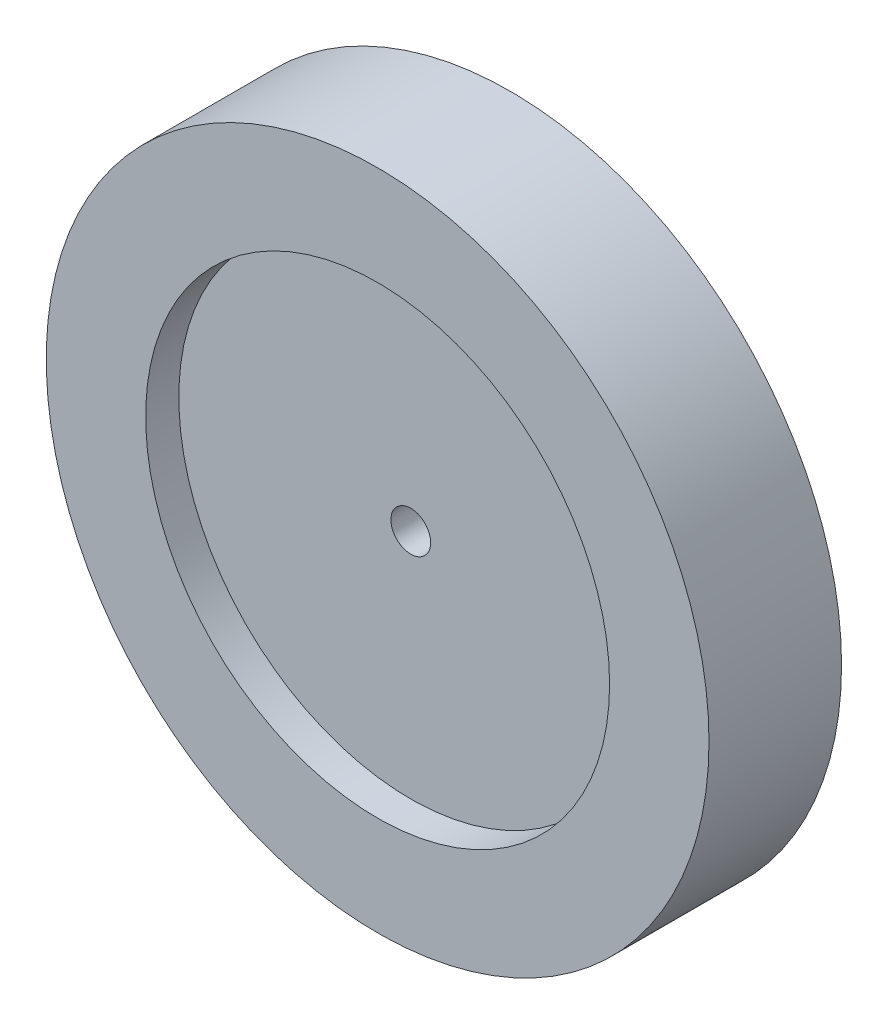
SolidWorks part; units mm, degrees
ref_plane "Front Plane" through (0, 0, 0) normal (0, 0, 1) x (1, 0, 0)
ref_plane "Top Plane" through (0, 0, 0) normal (0, 1, 0) x (1, 0, 0)
ref_plane "Right Plane" through (0, 0, 0) normal (1, 0, 0) x (0, 0, -1)
sketch "Sketch1" plane through (0, 0, 0) normal (0, 0, 1) x (1, 0, 0)
  circle A0 centre (0, 0) radius 50
  dimension "D1" = 100
extrude "Boss-Extrude1" add sketch "Sketch1" along normal mid plane 20
sketch "Sketch2" plane through (0, 0, 10) normal (0, 0, 1) x (1, 0, 0)
  circle A0 centre (0, 0) radius 35
  dimension "D1" = 70
extrude "Cut-Extrude1" cut sketch "Sketch2" against normal blind 5
mirror "Mirror1" about plane through (0, 0, 0) normal (0, 0, 1) of "Cut-Extrude1"
sketch "Sketch3" plane through (0, 0, -5) normal (0, 0, -1) x (-1, 0, 0)
  circle A0 centre (0, 0) radius 7.5
  dimension "D1" = 15
extrude "Boss-Extrude2" add sketch "Sketch3" along normal blind 20
sketch "Sketch4" plane through (0, 0, -25) normal (0, 0, -1) x (-1, 0, 0)
  circle A0 centre (0, 0) radius 3
  dimension "D1" = 6
extrude "Cut-Extrude2" cut sketch "Sketch4" against normal up to next
